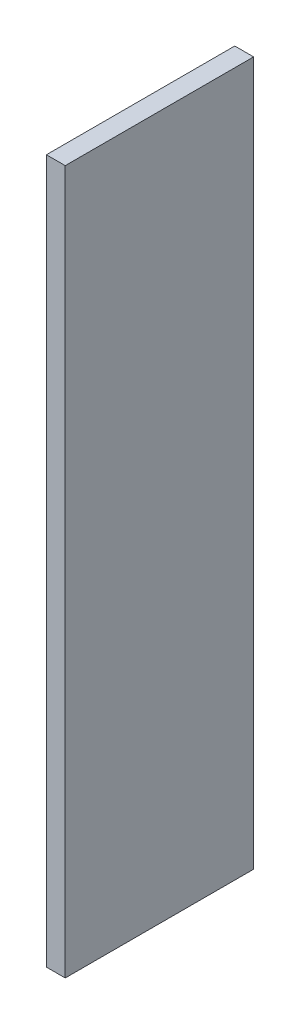
SolidWorks part; units mm, degrees
ref_plane "Front Plane" through (0, 0, 0) normal (0, 0, 1) x (1, 0, 0)
ref_plane "Top Plane" through (0, 0, 0) normal (0, 1, 0) x (1, 0, 0)
ref_plane "Right Plane" through (0, 0, 0) normal (1, 0, 0) x (0, 0, -1)
sketch "Sketch1" plane through (0, 0, 0) normal (1, 0, 0) x (0, 0, -1)
  line L1 (0, 0) -> (25.4, 0)
  line L2 (0, 0) -> (0, 94.869)
  line L3 (0, 94.869) -> (25.4, 94.869)
  line L4 (25.4, 0) -> (25.4, 94.869)
  dimension "D1" = 94.869
  dimension "D2" = 25.4
extrude "Boss-Extrude1" add sketch "Sketch1" along normal blind 2.54
